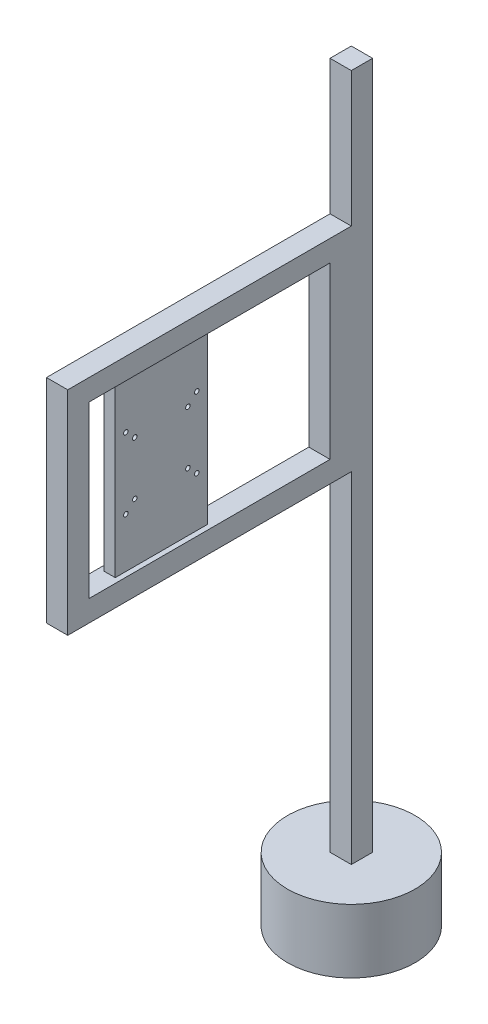
SolidWorks part; units mm, degrees
ref_plane "前基準面" through (0, 0, 0) normal (0, 0, 1) x (1, 0, 0)
ref_plane "上基準面" through (0, 0, 0) normal (0, 1, 0) x (1, 0, 0)
ref_plane "右基準面" through (0, 0, 0) normal (1, 0, 0) x (0, 0, -1)
sketch "草圖1" plane through (0, 0, 0) normal (0, 1, 0) x (1, 0, 0)
  circle A0 centre (0, 0) radius 90
  dimension "D1" = 180
extrude "填料-伸長1" add sketch "草圖1" along normal blind 90
sketch "草圖2" plane through (0, 90, 0) normal (0, 1, 0) x (1, 0, 0)
  line L1 (-15, -15) -> (15, -15)
  line L2 (-15, -15) -> (-15, 15)
  line L3 (-15, 15) -> (15, 15)
  line L4 (15, -15) -> (15, 15)
  line L5 (-15, -15) -> (15, 15) construction
  line L6 (-15, 15) -> (15, -15) construction
  point P0 (0, 0)
  dimension "D1" = 30
  dimension "D2" = 30
extrude "填料-伸長2" add sketch "草圖2" along normal blind 970
ref_plane "平面1" through (0, 0, 0) normal (-0.7071, 0, -0.7071) x (-0.7071, 0, 0.7071)
sketch "草圖3" plane through (0, 0, 0) normal (-0.7071, 0, -0.7071) x (-0.7071, 0, 0.7071)
  line L0 (0, 42.3009) -> (0, 361.2338) construction
  line L2 (-15, 180) -> (15, 180)
  line L3 (-15, 180) -> (-15, 210)
  line L4 (-15, 210) -> (15, 210)
  line L5 (15, 180) -> (15, 210)
  line L6 (-15, 180) -> (15, 210) construction
  line L7 (-15, 210) -> (15, 180) construction
  point P3 (0, 195)
  dimension "D1" = 30
  dimension "D2" = 30
  dimension "D3" = 105
extrude "填料-伸長3" add sketch "草圖3" along normal blind 200
sketch "草圖5" plane through (15, 0, 0) normal (1, 0, 0) x (0, 0, -1)
  line L0 (-15, 1060) -> (-15, 90) construction
  line L1 (-15, 870) -> (-415, 870)
  line L2 (-15, 870) -> (-15, 570)
  line L3 (-15, 570) -> (-415, 570)
  line L4 (-415, 870) -> (-415, 570)
  line L5 (-45, 840) -> (-385, 840)
  line L6 (-385, 840) -> (-385, 600)
  line L7 (-45, 600) -> (-385, 600)
  line L8 (-45, 840) -> (-45, 600)
  line L9 (90, 90) -> (-90, 90) construction
  dimension "D1" = 400
  dimension "D2" = 300
  dimension "D4" = 480
  dimension "D3" = 30
extrude "填料-伸長5" add sketch "草圖5" against normal blind 30
sketch "草圖7" plane through (-15, 0, 0) normal (-1, 0, 0) x (0, 0, 1)
  line L0 (45, 840) -> (385, 840) construction
  line L1 (341, 840) -> (211, 840)
  line L2 (341, 840) -> (341, 600)
  line L3 (341, 600) -> (211, 600)
  line L4 (211, 840) -> (211, 600)
  line L5 (385, 600) -> (45, 600) construction
  line L6 (385, 720) -> (-33.4547, 720) construction
  line L7 (276, 489) -> (276, 934) construction
  line L8 (137, 489) -> (415, 489) construction
  line L9 (415, 934) -> (137, 934) construction
  line L10 (385, 840) -> (385, 600) construction
  circle A0 centre (313.5, 757.5) radius 3.175
  circle A1 centre (238.5, 757.5) radius 3.175
  circle A2 centre (238.5, 682.5) radius 3.175
  circle A3 centre (313.5, 682.5) radius 3.175
  circle A4 centre (326, 770) radius 3.175
  circle A5 centre (226, 770) radius 3.175
  circle A6 centre (326, 670) radius 3.175
  circle A7 centre (226, 670) radius 3.175
  dimension "D3" = 6.35
  dimension "D6" = 6.35
  dimension "D8" = 50
  dimension "D1" = 65
  dimension "D2" = 65
  dimension "D4" = 37.5
  dimension "D5" = 37.5
  dimension "D7" = 50
extrude "填料-伸長6" add sketch "草圖7" against normal up to vertex (30 mm away)
sketch "草圖8" plane through (-15, 0, 0) normal (-1, 0, 0) x (0, 0, 1)
  line L1 (211, 840) -> (341, 840)
  line L2 (211, 840) -> (211, 600)
  line L3 (211, 600) -> (341, 600)
  line L4 (341, 840) -> (341, 600)
extrude "除料-伸長1" cut sketch "草圖8" against normal blind 7
sketch "草圖9" plane through (15, 0, 0) normal (1, 0, 0) x (0, 0, -1)
  line L0 (-211, 840) -> (-211, 600) construction
  line L1 (-341, 840) -> (-211, 840)
  line L2 (-341, 840) -> (-341, 600)
  line L3 (-341, 600) -> (-211, 600)
  line L4 (-211, 840) -> (-211, 600)
  line L5 (-211, 600) -> (-45, 600) construction
extrude "除料-伸長2" cut sketch "草圖9" against normal blind 7
